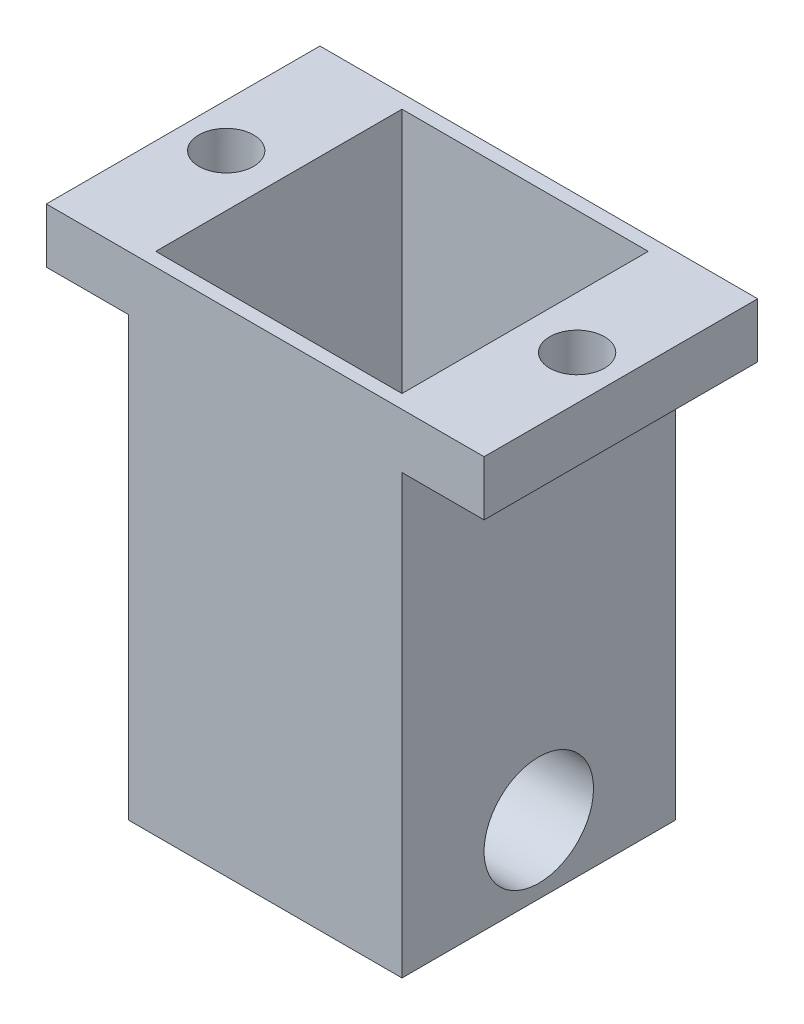
SolidWorks part; units mm, degrees
ref_plane "Front Plane" through (0, 0, 0) normal (0, 0, 1) x (1, 0, 0)
ref_plane "Top Plane" through (0, 0, 0) normal (0, 1, 0) x (1, 0, 0)
ref_plane "Right Plane" through (0, 0, 0) normal (1, 0, 0) x (0, 0, -1)
sketch "Sketch1" plane through (0, 0, 0) normal (0, 1, 0) x (1, 0, 0)
  line L1 (0, 0) -> (63.5, 0)
  line L2 (0, 0) -> (0, 63.5)
  line L3 (0, 63.5) -> (63.5, 63.5)
  line L4 (63.5, 0) -> (63.5, 63.5)
  dimension "D1" = 63.5
  dimension "D2" = 63.5
extrude "Boss-Extrude1" add sketch "Sketch1" along normal blind 31.75
sketch "Sketch2" plane through (0, 31.75, 0) normal (0, 1, 0) x (1, 0, 0)
  line L1 (0, 0) -> (63.5, 0)
  line L2 (0, 0) -> (0, 63.5)
  line L3 (0, 63.5) -> (63.5, 63.5)
  line L4 (63.5, 0) -> (63.5, 63.5)
  line L5 (3.175, 3.175) -> (60.325, 3.175)
  line L6 (3.175, 3.175) -> (3.175, 60.325)
  line L7 (3.175, 60.325) -> (60.325, 60.325)
  line L8 (60.325, 3.175) -> (60.325, 60.325)
  dimension "D1" = 3.175
  dimension "D2" = 3.175
  dimension "D3" = 3.175
  dimension "D4" = 3.175
extrude "Boss-Extrude2" add sketch "Sketch2" along normal blind 82.55
sketch "Sketch3" plane through (63.5, 0, 0) normal (1, 0, 0) x (0, 0, -1)
  line L0 (63.5, 114.3) -> (63.5, 0) construction
  line L1 (0, 114.3) -> (63.5, 114.3)
  line L2 (0, 114.3) -> (0, 101.6)
  line L3 (0, 101.6) -> (63.5, 101.6)
  line L4 (63.5, 114.3) -> (63.5, 101.6)
  dimension "D1" = 12.7
extrude "Boss-Extrude3" add sketch "Sketch3" along normal blind 19.05
ref_plane "Plane1" through (31.75, 0, 0) normal (1, 0, 0) x (0, 0, -1)
mirror "Mirror2" about plane through (31.75, 0, 0) normal (1, 0, 0) of "Boss-Extrude3"
hole_wizard "1 (1) Diameter Hole2" positions "Sketch4" profile "Sketch5" hole size "1" standard "ANSI Inch" end condition up to next
sketch "Sketch4" plane through (63.5, 0, 0) normal (1, 0, 0) x (0, 0, -1)
  line L0 (0, 0) -> (63.5, 0) construction
  point P0 (31.75, 15.875)
  point P7 (31.75, 0)
  dimension "D1" = 15.875
sketch "Sketch5" plane through (63.5, 15.875, -31.75) normal (0, 1, 0) x (0, 0, -1)
  line L0 (0, 0) -> (0, 63.5)
  line L1 (0, 63.5) -> (12.7, 63.5)
  line L2 (12.7, 63.5) -> (12.7, 0)
  line L5 (12.7, 0) -> (0, 0)
  line L11 (0, -6.35) -> (0, 107.95) construction
  dimension "Thru Hole Dia." = 25.4
  dimension "Thru Hole Depth" = 63.5
hole_wizard "1/2 (0.5) Diameter Hole1" positions "Sketch6" profile "Sketch7" hole size "1/2" standard "ANSI Inch" end condition up to next
sketch "Sketch6" plane through (0, 114.3, 0) normal (0, 1, 0) x (1, 0, 0)
  line L0 (82.55, 63.5) -> (82.55, 0) construction
  line L1 (31.75, -34.925) -> (31.75, 34.925) construction
  point P0 (72.39, 31.75)
  point P2 (-8.89, 31.5933)
  point P8 (82.55, 31.75)
  dimension "D1" = 81.28
  dimension "D2" = 40.64
sketch "Sketch7" plane through (72.39, 114.3, -31.75) normal (1, 0, 0) x (0, 0, 1)
  line L0 (0, 0) -> (0, 12.7)
  line L1 (0, 12.7) -> (6.35, 12.7)
  line L2 (6.35, 12.7) -> (6.35, 0)
  line L5 (6.35, 0) -> (0, 0)
  line L11 (0, -6.35) -> (0, 107.95) construction
  dimension "Thru Hole Dia." = 12.7
  dimension "Thru Hole Depth" = 12.7
